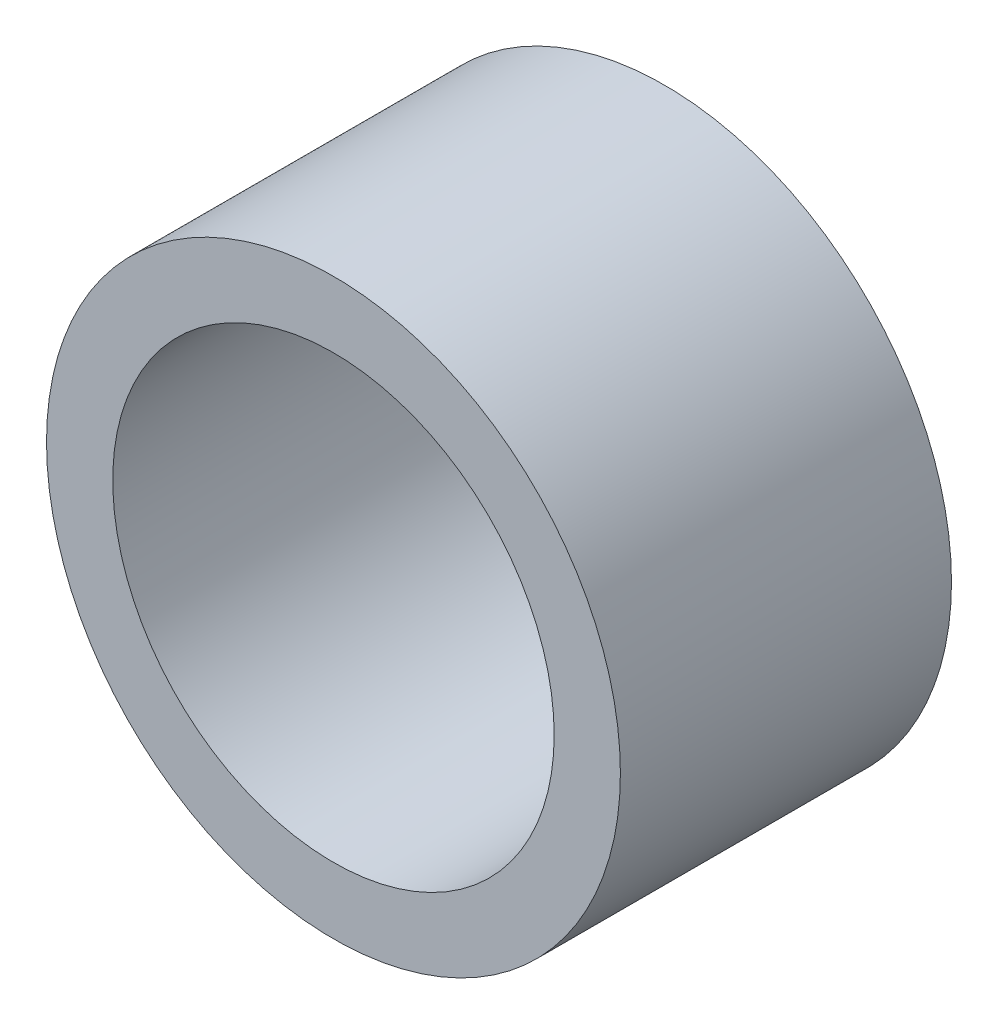
SolidWorks part; units mm, degrees
ref_plane "Front Plane" through (0, 0, 0) normal (0, 0, 1) x (1, 0, 0)
ref_plane "Top Plane" through (0, 0, 0) normal (0, 1, 0) x (1, 0, 0)
ref_plane "Right Plane" through (0, 0, 0) normal (1, 0, 0) x (0, 0, -1)
sketch "Sketch2" plane through (0, 0, 0) normal (0, 0, 1) x (1, 0, 0)
  circle A0 centre (0, 0) radius 13
  circle A1 centre (0, 0) radius 10
  dimension "D1" = 20
  dimension "D2" = 26
extrude "Boss-Extrude1" add sketch "Sketch2" along normal blind 15
